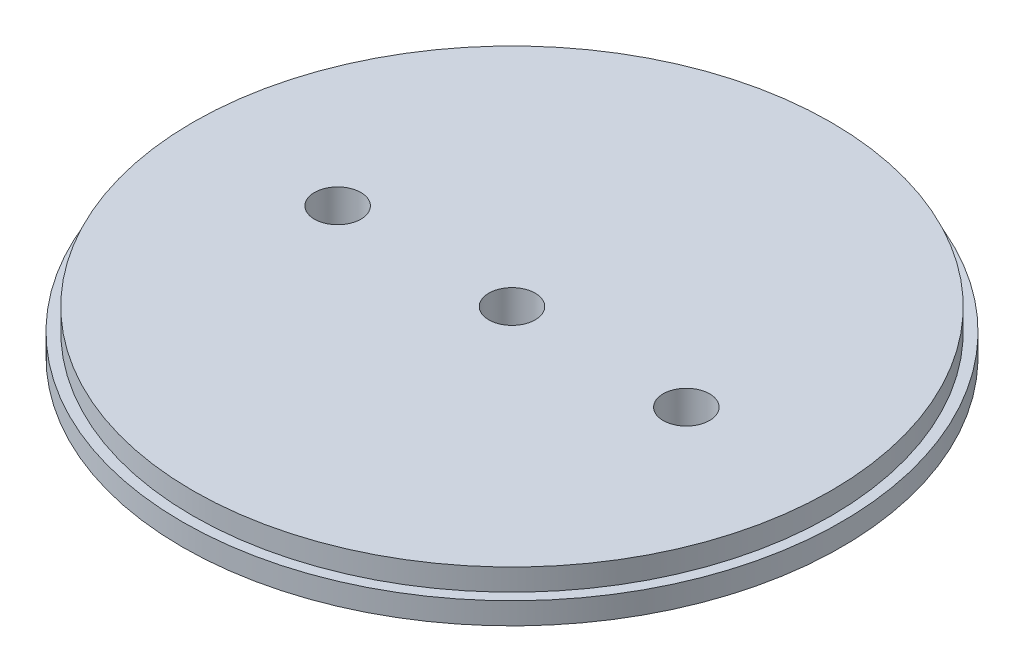
SolidWorks part; units mm, degrees
material "A-Glass Fiber"
ref_plane "Front Plane" through (0, 0, 0) normal (0, 0, 1) x (1, 0, 0)
ref_plane "Top Plane" through (0, 0, 0) normal (0, 1, 0) x (1, 0, 0)
ref_plane "Right Plane" through (0, 0, 0) normal (1, 0, 0) x (0, 0, -1)
sketch "Sketch1" plane through (0, 0, 0) normal (0, 1, 0) x (1, 0, 0)
  circle A0 centre (0, 0) radius 48.006
  dimension "D1" = 96.012
extrude "Boss-Extrude1" add sketch "Sketch1" along normal blind 3.175
sketch "Sketch2" plane through (0, 3.175, 0) normal (0, 1, 0) x (1, 0, 0)
  circle A0 centre (0, 0) radius 46.482
  dimension "D1" = 92.964
extrude "Boss-Extrude2" add sketch "Sketch2" along normal blind 3.175
sketch "Sketch3" plane through (0, 0, 0) normal (0, -1, 0) x (1, 0, 0)
  line L0 (-25.4, 0) -> (25.4, 0) construction
  point P2 (0, 0)
  dimension "D1" = 25.4
sketch "Sketch4" plane through (0, 0, 0) normal (0, -1, 0) x (-1, 0, 0)
  point P0 (-25.4, 0)
  point P3 (0, 0)
  point P6 (25.4, 0)
hole_wizard "1/4 Clearance Hole1" positions "Sketch4" profile "Sketch5" hole size "1/4" standard "ANSI Inch"
sketch "Sketch5" plane through (25.4, 0, 0) normal (1, 0, 0) x (0, 0, -1)
  line L0 (0, 0) -> (0, 50.8)
  line L1 (0, 50.8) -> (3.3782, 48.7702)
  line L2 (3.3782, 48.7702) -> (3.3782, 0)
  line L5 (3.3782, 0) -> (0, 0)
  line L10 (0, 50.8) -> (-3.3782, 48.7702) construction
  line L11 (0, -6.35) -> (0, 107.95) construction
  dimension "Hole Dia." = 6.7564
  dimension "Hole Depth" = 50.8
  dimension "Drill Angle" = 118
